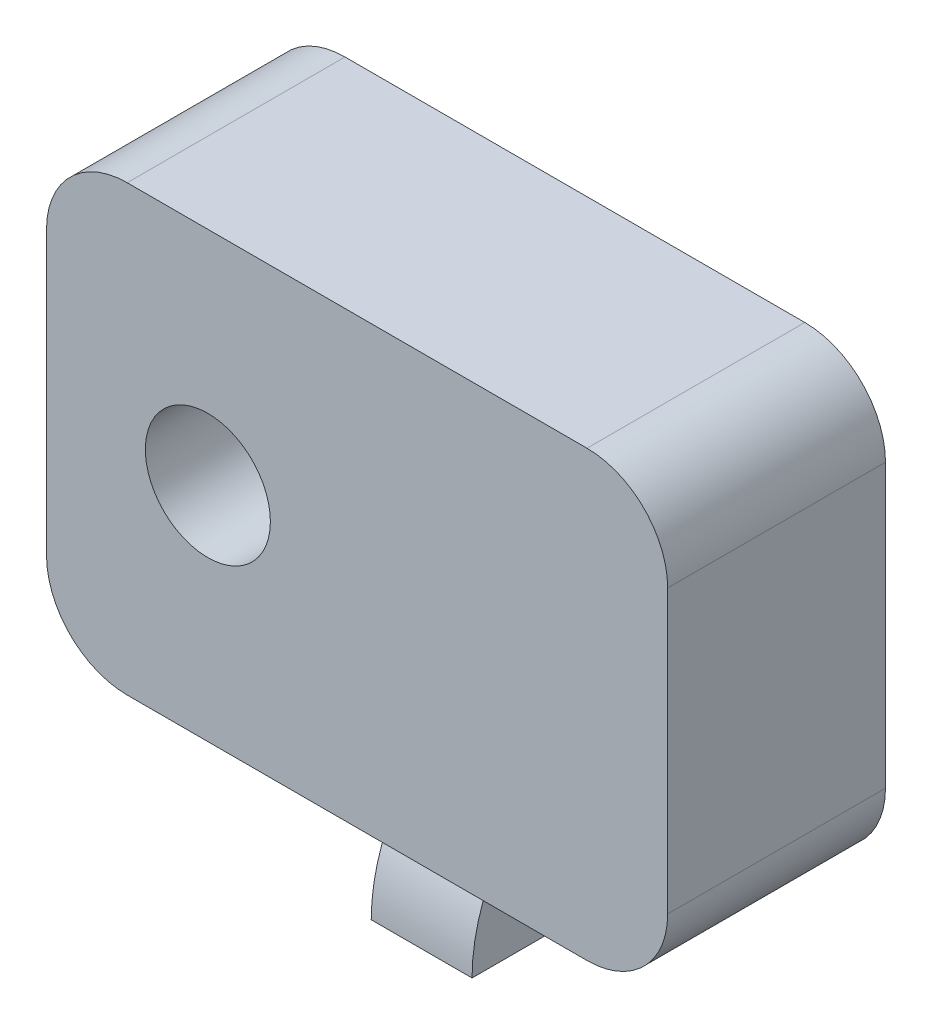
SolidWorks part; units mm, degrees
ref_plane "Front Plane" through (0, 0, 0) normal (0, 0, 1) x (1, 0, 0)
ref_plane "Top Plane" through (0, 0, 0) normal (0, 1, 0) x (1, 0, 0)
ref_plane "Right Plane" through (0, 0, 0) normal (1, 0, 0) x (0, 0, -1)
sketch "Sketch1" plane through (0, 0, 0) normal (0, 0, 1) x (1, 0, 0)
  line L1 (0, 0) -> (-77, 0)
  line L2 (0, 0) -> (0, 55)
  line L3 (0, 55) -> (-77, 55)
  line L4 (-77, 0) -> (-77, 55)
  dimension "D1" = 77
  dimension "D2" = 55
extrude "Boss-Extrude1" add sketch "Sketch1" along normal blind 27
fillet "Fillet1" radius 10 4 edges at (-77, 0, 13.5) (0, 0, 13.5) (-77, 55, 13.5) (0, 55, 13.5)
sketch "Sketch2" plane through (0, 0, 0) normal (1, 0, 0) x (0, 0, -1)
  line L0 (-2, 0) -> (-2, -11)
  line L1 (0, 0) -> (-27, 0) construction
  line L2 (-8.3085, -17) -> (-19, -17)
  line L3 (-16, -6) -> (-16, 0)
  line L4 (-16, 0) -> (-2, 0)
  line L5 (-19, -17) -> (-19, -24.8611) construction
  line L6 (-9, 0) -> (-9, -17) construction
  line L7 (-7.8402, 0) -> (-7.8402, -17.2529) construction
  line L8 (-4.7402, -11.7006) -> (-4.7402, -14.6467)
  arc A0 (-2, -11) -> (-8.3085, -17) centre (-5.9402, -13.1736) cw
  arc A1 (-19, -17) -> (-16, -6) centre (2.6667, -17) cw
  arc A2 (-4.7402, -11.7006) -> (-4.7402, -14.6467) centre (-5.9402, -13.1736) ccw
  dimension "D4" = 11
  dimension "D6" = 4.5
  dimension "D9" = 3.8
  dimension "D1" = 2
  dimension "D2" = 14
  dimension "D3" = 17
  dimension "D5" = 17
  dimension "D7" = 11
  dimension "D8" = 10.6915
  dimension "D10" = 3.1
extrude "Boss-Extrude2" add sketch "Sketch2" along normal blind 12.5 from offset 44.75 offset against normal yes
sketch "Sketch3" plane through (0, 0, 27) normal (0, 0, 1) x (1, 0, 0)
  line L0 (0, 10) -> (0, 45) construction
  circle A0 centre (-57, 27.5) radius 7.75
  point P4 (0, 27.5)
  dimension "D2" = 15.5
  dimension "D1" = 57
extrude "Cut-Extrude1" cut sketch "Sketch3" against normal blind 12.5
